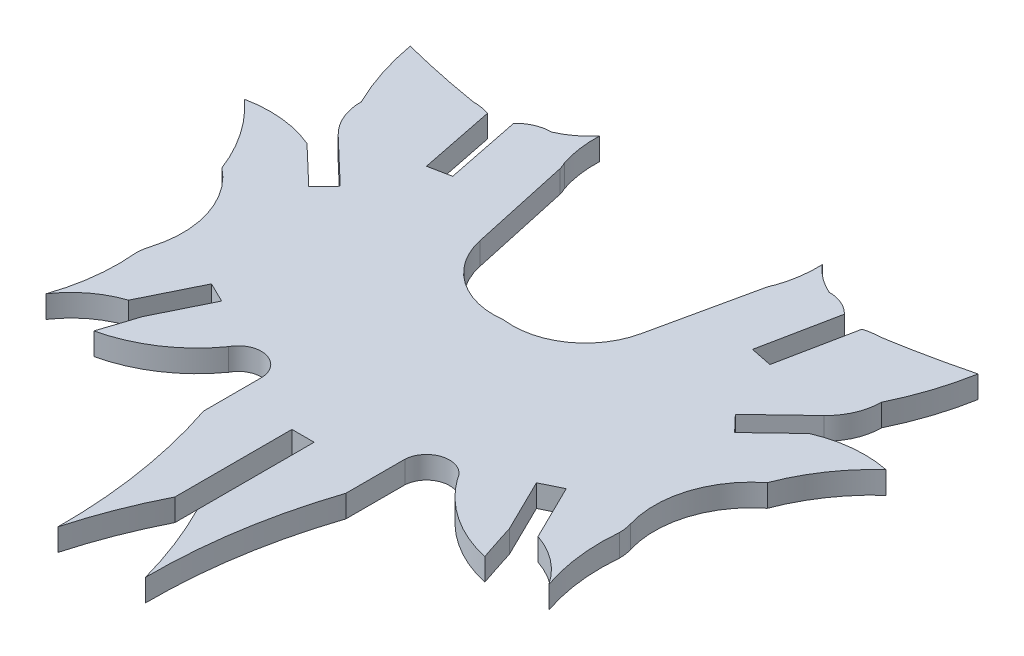
SolidWorks part; units mm, degrees
ref_plane "Front Plane" through (0, 0, 0) normal (0, 0, 1) x (1, 0, 0)
ref_plane "Top Plane" through (0, 0, 0) normal (0, 1, 0) x (1, 0, 0)
ref_plane "Right Plane" through (0, 0, 0) normal (1, 0, 0) x (0, 0, -1)
sketch "Sketch1" plane through (0, 0, 0) normal (0, 1, 0) x (1, 0, 0)
  line L0 (5.5206, 10.563) -> (7.0507, 17.5712)
  line L1 (11.3339, 18.6988) -> (10.2775, 13.4572)
  line L2 (10.2775, 13.4572) -> (11.7737, 13.1552)
  line L3 (11.7737, 13.1552) -> (12.8288, 18.3998)
  line L4 (16.6519, 11.9791) -> (13.5441, 9.0124)
  line L5 (13.5441, 9.0124) -> (14.5991, 7.9086)
  line L6 (14.5991, 7.9086) -> (17.2219, 10.4112)
  line L7 (14.035, -5.0061) -> (12.1612, -1.1976)
  line L8 (12.1612, -1.1976) -> (10.7921, -1.8711)
  line L9 (10.7921, -1.8711) -> (12.5824, -5.5152)
  line L10 (4.8803, -4.977) -> (4.8786, -9.0223)
  line L11 (0.762, -15.0993) -> (0.762, -7.0819)
  line L12 (0.762, -7.0819) -> (-0.762, -7.0819)
  line L13 (-0.762, -7.0819) -> (-0.762, -15.1003)
  line L14 (-5.5206, 10.563) -> (-7.0507, 17.5712)
  line L15 (-11.3339, 18.6988) -> (-10.2775, 13.4572)
  line L16 (-10.2775, 13.4572) -> (-11.7737, 13.1552)
  line L17 (-11.7737, 13.1552) -> (-12.8288, 18.3998)
  line L18 (-16.6519, 11.9791) -> (-13.5441, 9.0124)
  line L19 (-13.5441, 9.0124) -> (-14.5991, 7.9086)
  line L20 (-14.5991, 7.9086) -> (-17.2219, 10.4112)
  line L21 (-14.035, -5.0061) -> (-12.1612, -1.1976)
  line L22 (-12.1612, -1.1976) -> (-10.7921, -1.8711)
  line L23 (-10.7921, -1.8711) -> (-12.5824, -5.5152)
  line L24 (-4.8803, -4.977) -> (-4.8786, -9.0223)
  arc A0 (0.0006, 6.6785) -> (5.5206, 10.563) centre (0.6448, 11.6274) ccw
  arc A1 (11.3339, 18.6988) -> (9.5049, 19.4797) centre (9.5049, 16.9474) ccw
  arc A2 (16.6519, 11.9791) -> (17.8379, 14.7514) centre (14.0047, 14.7514) ccw
  arc A3 (18.6986, 6.0555) -> (16.4572, -1.0833) centre (22.8232, 0.8392) ccw
  arc A4 (16.5894, -1.9751) -> (16.4572, -1.0833) centre (13.5139, -1.9751) ccw
  arc A5 (7.8469, -4.3357) -> (4.8803, -4.977) centre (6.4524, -5.0672) ccw
  arc A6 (17.8379, 14.7514) -> (19.4639, 19.7306) centre (0.7346, 23.0919) ccw
  arc A7 (14.0047, 18.5846) -> (19.4639, 19.7306) centre (3.6577, 81.4527) ccw
  arc A8 (7.6375, 20.8787) -> (9.5049, 19.4797) centre (11.6248, 24.2552) ccw
  arc A9 (7.2386, 18.0771) -> (7.6375, 20.8787) centre (-0.2564, 20.5733) ccw
  arc A10 (7.2386, 18.0771) -> (7.0507, 17.5712) centre (9.5049, 16.9474) ccw
  arc A11 (14.0047, 18.5846) -> (12.8288, 18.3998) centre (14.0047, 14.7514) ccw
  arc A12 (21.9936, 10.894) -> (17.2219, 10.4112) centre (20.382, 3.0002) ccw
  arc A13 (21.9936, 10.894) -> (18.6986, 6.0555) centre (30.3868, 1.637) ccw
  arc A14 (16.5894, -1.9751) -> (17.2433, -7.4616) centre (29.6622, -3.1993) ccw
  arc A15 (17.2433, -7.4616) -> (14.035, -5.0061) centre (12.0353, -10.9424) ccw
  arc A16 (7.8469, -4.3357) -> (13.4014, -8.0221) centre (15.4627, 1.1117) ccw
  arc A17 (12.5824, -5.5152) -> (13.4014, -8.0221) centre (121.1893, 28.5819) ccw
  arc A18 (4.8786, -9.0223) -> (2.9987, -20.8787) centre (39.777, -20.6331) ccw
  arc A19 (2.9987, -20.8787) -> (0.762, -15.0993) centre (-27.2755, -29.2724) ccw
  arc A20 (-5.5206, 10.563) -> (0.0006, 6.6785) centre (-0.6448, 11.6272) ccw
  arc A21 (-9.5049, 19.4797) -> (-11.3339, 18.6988) centre (-9.5049, 16.9474) ccw
  arc A22 (-7.0507, 17.5712) -> (-7.2386, 18.0771) centre (-9.5049, 16.9474) ccw
  arc A23 (-17.8379, 14.7514) -> (-16.6519, 11.9791) centre (-14.0047, 14.7514) ccw
  arc A24 (-12.8288, 18.3998) -> (-14.0047, 18.5846) centre (-14.0047, 14.7514) ccw
  arc A25 (-16.4572, -1.0833) -> (-18.6986, 6.0555) centre (-22.8232, 0.8392) ccw
  arc A26 (-16.4572, -1.0833) -> (-16.5894, -1.9751) centre (-13.5139, -1.9751) ccw
  arc A27 (-4.8803, -4.977) -> (-7.8469, -4.3357) centre (-6.4524, -5.0672) ccw
  arc A28 (-19.4639, 19.7306) -> (-17.8379, 14.7514) centre (-0.7346, 23.0919) ccw
  arc A29 (-19.4639, 19.7306) -> (-14.0047, 18.5846) centre (-3.6577, 81.4527) ccw
  arc A30 (-9.5049, 19.4797) -> (-7.6375, 20.8787) centre (-11.6248, 24.2552) ccw
  arc A31 (-7.6375, 20.8787) -> (-7.2386, 18.0771) centre (0.2564, 20.5733) ccw
  arc A32 (-17.2219, 10.4112) -> (-21.9936, 10.894) centre (-20.382, 3.0002) ccw
  arc A33 (-18.6986, 6.0555) -> (-21.9936, 10.894) centre (-30.3868, 1.637) ccw
  arc A34 (-17.2433, -7.4616) -> (-16.5894, -1.9751) centre (-29.6622, -3.1993) ccw
  arc A35 (-14.035, -5.0061) -> (-17.2433, -7.4616) centre (-12.0353, -10.9424) ccw
  arc A36 (-13.4014, -8.0221) -> (-7.8469, -4.3357) centre (-15.4627, 1.1117) ccw
  arc A37 (-13.4014, -8.0221) -> (-12.5824, -5.5152) centre (-121.1893, 28.5819) ccw
  arc A38 (-2.9987, -20.8787) -> (-4.8786, -9.0223) centre (-39.777, -20.6331) ccw
  arc A39 (-0.762, -15.1003) -> (-2.9987, -20.8787) centre (27.2749, -29.2746) ccw
extrude "Boss-Extrude1" add sketch "Sketch1" along normal blind 1.524
